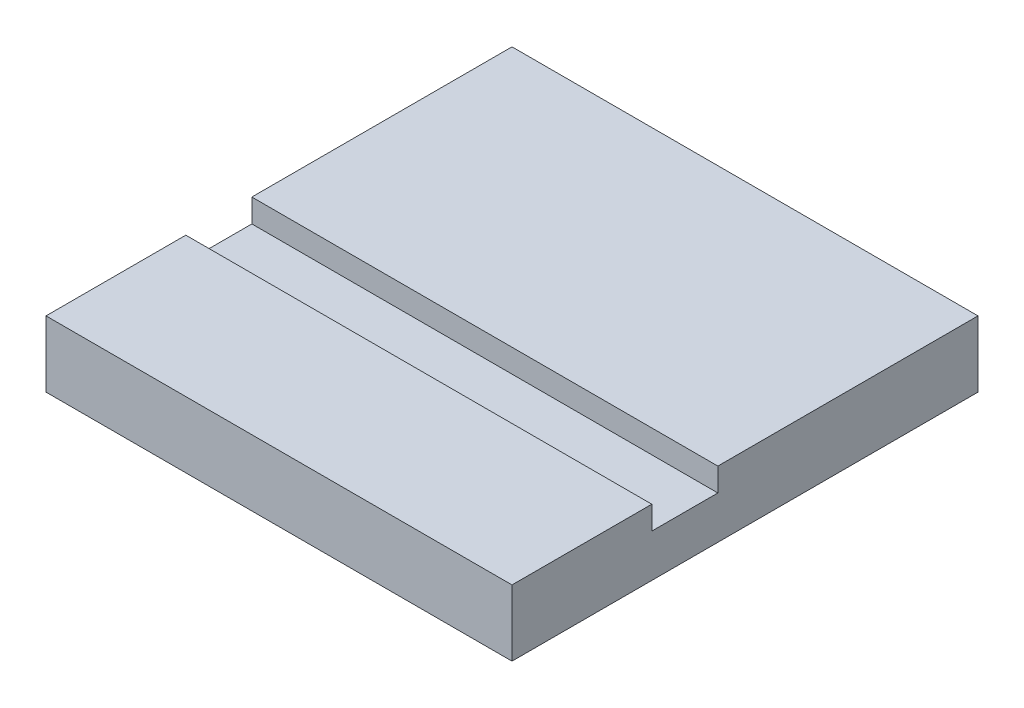
SolidWorks part; units mm, degrees
ref_plane "Front Plane" through (0, 0, 0) normal (0, 0, 1) x (1, 0, 0)
ref_plane "Top Plane" through (0, 0, 0) normal (0, 1, 0) x (1, 0, 0)
ref_plane "Right Plane" through (0, 0, 0) normal (1, 0, 0) x (0, 0, -1)
sketch "Sketch1" plane through (0, 0, 0) normal (0, 1, 0) x (1, 0, 0)
  line L1 (63.5, 63.5) -> (-63.5, 63.5)
  line L2 (63.5, 63.5) -> (63.5, -63.5)
  line L3 (63.5, -63.5) -> (-63.5, -63.5)
  line L4 (-63.5, 63.5) -> (-63.5, -63.5)
  line L5 (63.5, 63.5) -> (-63.5, -63.5) construction
  line L6 (63.5, -63.5) -> (-63.5, 63.5) construction
  point P0 (0, 0)
  dimension "D1" = 127
  dimension "D2" = 127
extrude "Boss-Extrude1" add sketch "Sketch1" along normal blind 18
sketch "Sketch2" plane through (0, 18, 0) normal (0, 1, 0) x (1, 0, 0)
  line L0 (-63.5, 63.5) -> (-63.5, -63.5) construction
  line L1 (-63.5, -25.4) -> (63.5, -25.4)
  line L2 (-63.5, -25.4) -> (-63.5, -7.4)
  line L3 (-63.5, -7.4) -> (63.5, -7.4)
  line L4 (63.5, -25.4) -> (63.5, -7.4)
  line L5 (63.5, -63.5) -> (63.5, 63.5) construction
  line L6 (-63.5, -63.5) -> (63.5, -63.5) construction
  dimension "D1" = 18
  dimension "D2" = 38.1
extrude "Cut-Extrude1" cut sketch "Sketch2" against normal blind 6.35
